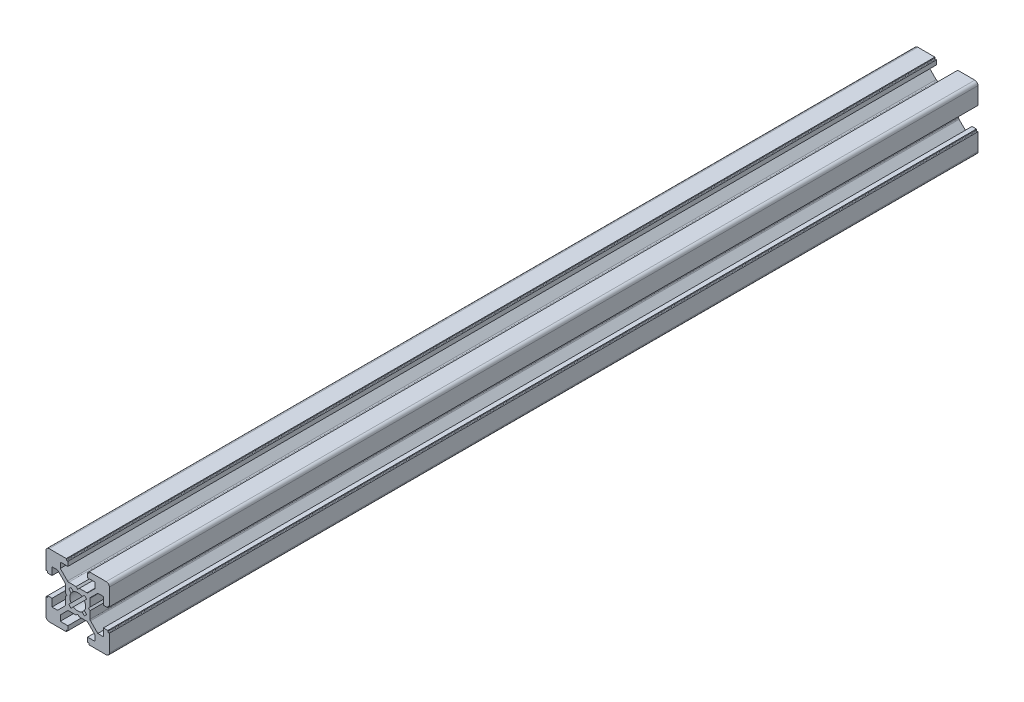
SolidWorks part; units mm, degrees
ref_plane "Спереди" through (0, 0, 0) normal (0, 0, 1) x (1, 0, 0)
ref_plane "Сверху" through (0, 0, 0) normal (0, 1, 0) x (1, 0, 0)
ref_plane "Справа" through (0, 0, 0) normal (1, 0, 0) x (0, 0, -1)
sketch "Sketch1" plane through (0, 0, 0) normal (0, 0, 1) x (1, 0, 0)
  line L0 (0, 10) -> (0, -10) construction
  line L1 (-10, -10) -> (10, -10) construction
  line L2 (-10, -10) -> (-10, 10) construction
  line L3 (-10, 10) -> (10, 10) construction
  line L4 (10, -10) -> (10, 10) construction
  line L5 (-10, -10) -> (10, 10) construction
  line L6 (-10, 10) -> (10, -10) construction
  line L7 (-10, 0) -> (10, 0) construction
  line L8 (0, 3.9) -> (-2.8444, 3.9)
  line L9 (-3.1979, 4.0464) -> (-5.5, 6.3485)
  line L10 (-5.5, 6.3485) -> (-5.5, 8.1)
  line L11 (-5.5, 8.1) -> (-3.1, 8.1)
  line L12 (-3.1, 8.1) -> (-3.1, 9.5)
  line L13 (-3.1, 9.5) -> (-3.4, 9.5)
  line L14 (-3.6, 9.7) -> (-3.6, 10)
  line L15 (-3.6, 10) -> (-9, 10)
  line L16 (-10, 3.6) -> (-10, 9)
  line L17 (-9.7, 3.6) -> (-10, 3.6)
  line L18 (-9.5, 3.1) -> (-9.5, 3.4)
  line L19 (-8.1, 3.1) -> (-9.5, 3.1)
  line L20 (-8.1, 5.5) -> (-8.1, 3.1)
  line L21 (-6.3485, 5.5) -> (-8.1, 5.5)
  line L22 (-4.0464, 3.1979) -> (-6.3485, 5.5)
  line L23 (-3.9, 0) -> (-3.9, 2.8444)
  line L24 (3.9, 0) -> (3.9, 2.8444)
  line L25 (4.0464, 3.1979) -> (6.3485, 5.5)
  line L26 (6.3485, 5.5) -> (8.1, 5.5)
  line L27 (8.1, 5.5) -> (8.1, 3.1)
  line L28 (8.1, 3.1) -> (9.5, 3.1)
  line L29 (9.5, 3.1) -> (9.5, 3.4)
  line L30 (9.7, 3.6) -> (10, 3.6)
  line L31 (10, 3.6) -> (10, 9)
  line L32 (3.6, 10) -> (9, 10)
  line L33 (3.6, 9.7) -> (3.6, 10)
  line L34 (3.1, 9.5) -> (3.4, 9.5)
  line L35 (3.1, 8.1) -> (3.1, 9.5)
  line L36 (5.5, 8.1) -> (3.1, 8.1)
  line L37 (5.5, 6.3485) -> (5.5, 8.1)
  line L38 (3.1979, 4.0464) -> (5.5, 6.3485)
  line L39 (0, 3.9) -> (2.8444, 3.9)
  line L40 (0, -3.9) -> (2.8444, -3.9)
  line L41 (3.1979, -4.0464) -> (5.5, -6.3485)
  line L42 (5.5, -6.3485) -> (5.5, -8.1)
  line L43 (5.5, -8.1) -> (3.1, -8.1)
  line L44 (3.1, -8.1) -> (3.1, -9.5)
  line L45 (3.1, -9.5) -> (3.4, -9.5)
  line L46 (3.6, -9.7) -> (3.6, -10)
  line L47 (3.6, -10) -> (9, -10)
  line L48 (10, -3.6) -> (10, -9)
  line L49 (9.7, -3.6) -> (10, -3.6)
  line L50 (9.5, -3.1) -> (9.5, -3.4)
  line L51 (8.1, -3.1) -> (9.5, -3.1)
  line L52 (8.1, -5.5) -> (8.1, -3.1)
  line L53 (6.3485, -5.5) -> (8.1, -5.5)
  line L54 (4.0464, -3.1979) -> (6.3485, -5.5)
  line L55 (3.9, 0) -> (3.9, -2.8444)
  line L56 (-3.9, 0) -> (-3.9, -2.8444)
  line L57 (-4.0464, -3.1979) -> (-6.3485, -5.5)
  line L58 (-6.3485, -5.5) -> (-8.1, -5.5)
  line L59 (-8.1, -5.5) -> (-8.1, -3.1)
  line L60 (-8.1, -3.1) -> (-9.5, -3.1)
  line L61 (-9.5, -3.1) -> (-9.5, -3.4)
  line L62 (-9.7, -3.6) -> (-10, -3.6)
  line L63 (-10, -3.6) -> (-10, -9)
  line L64 (-3.6, -10) -> (-9, -10)
  line L65 (-3.6, -9.7) -> (-3.6, -10)
  line L66 (-3.1, -9.5) -> (-3.4, -9.5)
  line L67 (-3.1, -8.1) -> (-3.1, -9.5)
  line L68 (-5.5, -8.1) -> (-3.1, -8.1)
  line L69 (-5.5, -6.3485) -> (-5.5, -8.1)
  line L70 (-3.1979, -4.0464) -> (-5.5, -6.3485)
  line L71 (0, -3.9) -> (-2.8444, -3.9)
  line L72 (2.0856, -1.3785) -> (2.8284, -2.1213)
  line L73 (2.0856, 1.3785) -> (2.8284, 2.1213)
  line L74 (2.8284, 2.1213) -> (2.1213, 2.8284)
  line L75 (2.1213, -2.8284) -> (2.8284, -2.1213)
  line L76 (1.3785, -2.0856) -> (2.1213, -2.8284)
  line L77 (1.3785, 2.0856) -> (2.1213, 2.8284)
  line L78 (-1.3785, -2.0856) -> (-2.1213, -2.8284)
  line L79 (-2.8284, -2.1213) -> (-2.1213, -2.8284)
  line L80 (-2.0856, -1.3785) -> (-2.8284, -2.1213)
  line L81 (-2.0856, 1.3785) -> (-2.8284, 2.1213)
  line L82 (-2.1213, 2.8284) -> (-2.8284, 2.1213)
  line L83 (-1.3785, 2.0856) -> (-2.1213, 2.8284)
  line L84 (-0.5, 3.9) -> (0, 3.4)
  line L85 (0, 3.4) -> (0.5, 3.9)
  line L86 (3.9, 0.5) -> (3.4, 0)
  line L87 (3.4, 0) -> (3.9, -0.5)
  line L88 (0.5, -3.9) -> (0, -3.4)
  line L89 (0, -3.4) -> (-0.5, -3.9)
  line L90 (-3.9, -0.5) -> (-3.4, 0)
  line L91 (-3.4, 0) -> (-3.9, 0.5)
  circle A0 centre (0, 0) radius 2.5
  arc A1 (-9, 10) -> (-10, 9) centre (-9, 9) ccw
  arc A2 (-2.8444, 3.9) -> (-3.1979, 4.0464) centre (-2.8444, 4.4) cw
  arc A3 (-3.4, 9.5) -> (-3.6, 9.7) centre (-3.4, 9.7) cw
  arc A4 (-9.5, 3.4) -> (-9.7, 3.6) centre (-9.7, 3.4) ccw
  arc A5 (-3.9, 2.8444) -> (-4.0464, 3.1979) centre (-4.4, 2.8444) ccw
  arc A6 (10, 9) -> (9, 10) centre (9, 9) ccw
  arc A7 (3.9, 2.8444) -> (4.0464, 3.1979) centre (4.4, 2.8444) cw
  arc A8 (9.5, 3.4) -> (9.7, 3.6) centre (9.7, 3.4) cw
  arc A9 (3.4, 9.5) -> (3.6, 9.7) centre (3.4, 9.7) ccw
  arc A10 (2.8444, 3.9) -> (3.1979, 4.0464) centre (2.8444, 4.4) ccw
  arc A11 (9, -10) -> (10, -9) centre (9, -9) ccw
  arc A12 (2.8444, -3.9) -> (3.1979, -4.0464) centre (2.8444, -4.4) cw
  arc A13 (3.4, -9.5) -> (3.6, -9.7) centre (3.4, -9.7) cw
  arc A14 (9.5, -3.4) -> (9.7, -3.6) centre (9.7, -3.4) ccw
  arc A15 (3.9, -2.8444) -> (4.0464, -3.1979) centre (4.4, -2.8444) ccw
  arc A16 (-10, -9) -> (-9, -10) centre (-9, -9) ccw
  arc A17 (-3.9, -2.8444) -> (-4.0464, -3.1979) centre (-4.4, -2.8444) cw
  arc A18 (-9.5, -3.4) -> (-9.7, -3.6) centre (-9.7, -3.4) cw
  arc A19 (-3.4, -9.5) -> (-3.6, -9.7) centre (-3.4, -9.7) ccw
  arc A20 (-2.8444, -3.9) -> (-3.1979, -4.0464) centre (-2.8444, -4.4) ccw
  point P0 (0, 0)
  point P42 (0, 0)
  point P70 (0, 0)
  point P98 (0, 0)
  point P126 (0, 0)
  point P139 (0, 0)
  point P152 (0, 0)
  dimension "D3" = 5
  dimension "D4" = 2
  dimension "D12" = 0.5
  dimension "D13" = 0.2
  dimension "D15" = 1
  dimension "D1" = 20
  dimension "D2" = 20
  dimension "D5" = 6.2
  dimension "D6" = 7.2
  dimension "D7" = 1.9
  dimension "D8" = 0.5
  dimension "D10" = 1.2
  dimension "D11" = 6.1
  dimension "D16" = 3.5
  dimension "D18" = 0.5
  dimension "D14" = 4
  dimension "D17" = 4
  dimension "D19" = 4
extrude "Extrude1" add sketch "Sketch1" along normal blind 274 contours A20 L71 L89 L88 L40 A12 L41 L42 L43 L44 L45 A13 L46 L47 A11 L48 L49 A14 L50 L51 L52 L53 L54 A15 L55 L87 L86 L24 A7 L25 L26 L27 L28 L29 A8 L30 L31 A6 L32 L33 A9 L34 L35 L36 L37 L38 A10 L39 L85 L84 L8
